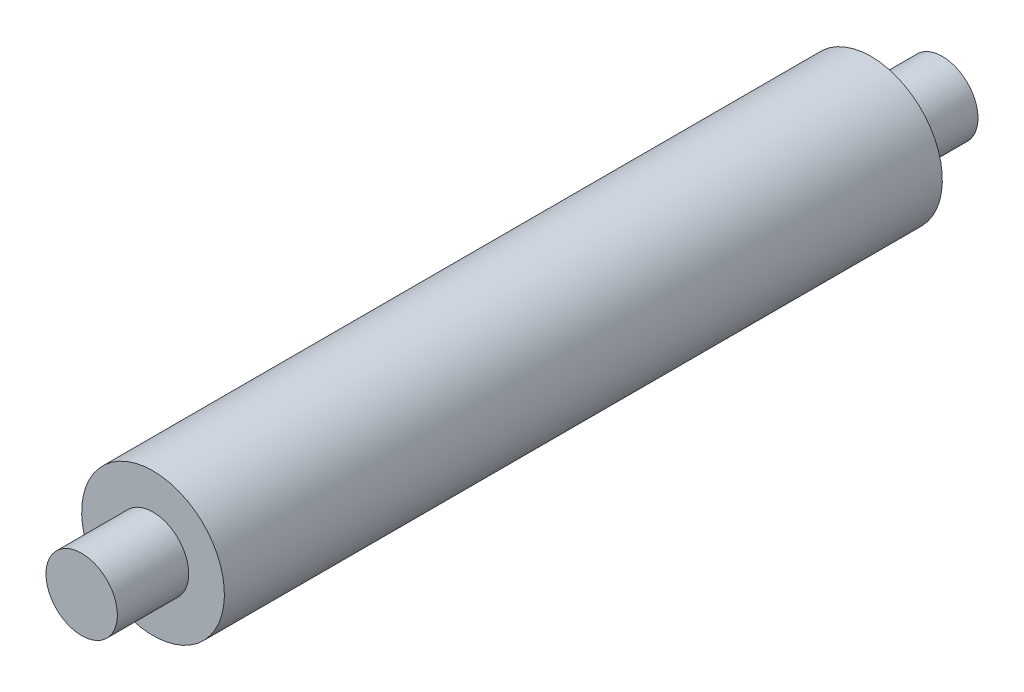
SolidWorks part; units mm, degrees
ref_plane "Front Plane" through (0, 0, 0) normal (0, 0, 1) x (1, 0, 0)
ref_plane "Top Plane" through (0, 0, 0) normal (0, 1, 0) x (1, 0, 0)
ref_plane "Right Plane" through (0, 0, 0) normal (1, 0, 0) x (0, 0, -1)
sketch "Sketch1" plane through (0, 0, 0) normal (1, 0, 0) x (0, 0, -1)
  line L1 (0, 0) -> (-127.762, 0)
  line L2 (0, 0) -> (0, 12.7)
  line L3 (0, 12.7) -> (-127.762, 12.7)
  line L4 (-127.762, 0) -> (-127.762, 12.7)
  line L5 (0, 0) -> (12.7, 0)
  line L6 (0, 0) -> (0, 6.35)
  line L7 (0, 6.35) -> (12.7, 6.35)
  line L8 (12.7, 0) -> (12.7, 6.35)
  line L9 (-127.762, 0) -> (-140.462, 0)
  line L10 (-127.762, 0) -> (-127.762, 6.35)
  line L11 (-127.762, 6.35) -> (-140.462, 6.35)
  line L12 (-140.462, 0) -> (-140.462, 6.35)
  dimension "D1" = 153.162
  dimension "D2" = 12.7
  dimension "D3" = 6.35
  dimension "D4" = 12.7
revolve "Revolve1" add sketch "Sketch1" angle 360 about L1
